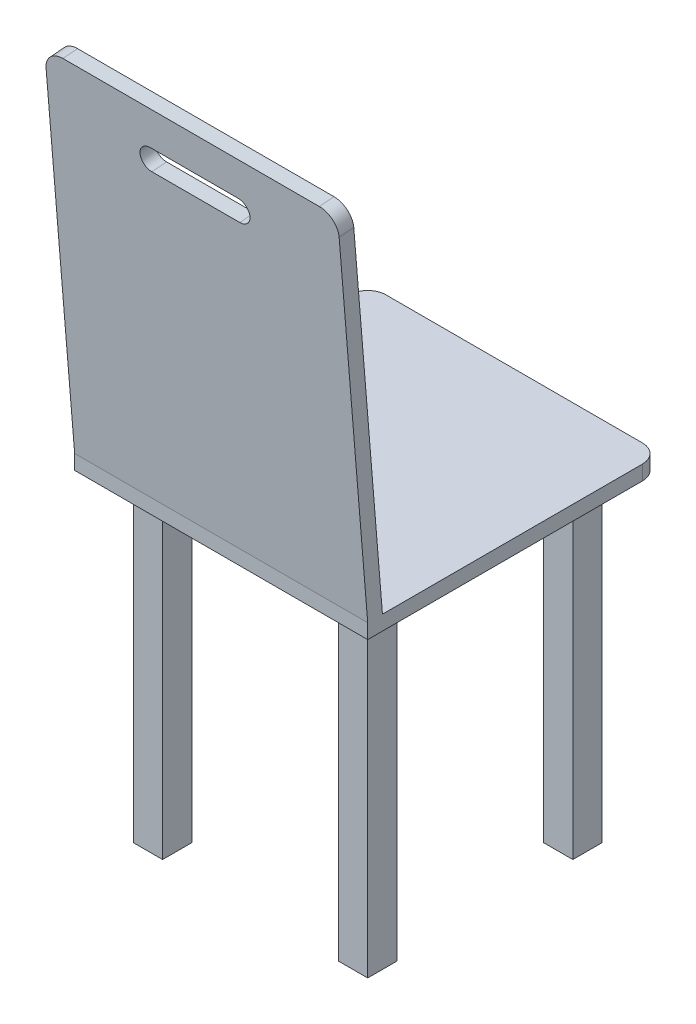
SolidWorks part; units mm, degrees
material "Beech"
ref_plane "Front Plane" through (0, 0, 0) normal (0, 0, 1) x (1, 0, 0)
ref_plane "Top Plane" through (0, 0, 0) normal (0, 1, 0) x (1, 0, 0)
ref_plane "Right Plane" through (0, 0, 0) normal (1, 0, 0) x (0, 0, -1)
sketch "Sketch3" plane through (0, 0, 0) normal (1, 0, 0) x (0, 0, -1)
  line L0 (0, 0) -> (40, 0)
  line L1 (40, 0) -> (40, 2)
  line L2 (40, 2) -> (2.0135, 2)
  line L3 (0, 2) -> (0, 0)
  line L4 (0, 2) -> (-4.1049, 52)
  line L5 (-4.1049, 52) -> (-2.1049, 52.1642)
  line L6 (-2.1049, 52.1642) -> (2.0135, 2)
  dimension "D1" = 40
  dimension "D2" = 50
  dimension "D3" = 2
  dimension "D4" = 2
extrude "Boss-Extrude2" add sketch "Sketch3" along normal blind 40
fillet "Fillet3" radius 2.5 4 edges at (40, 1, -40) (0, 1, -40) (0, 52.0821, 3.1049) (40, 52.0821, 3.1049)
sketch "Sketch5" plane through (0, 0.0134, -0.1631) normal (0, -0.0818, 0.9966) x (1, 0, 0)
  line L0 (14, 47.1615) -> (26, 47.1615)
  line L1 (26, 44.1615) -> (14, 44.1615)
  line L2 (0, 49.6615) -> (0, 1.9933) construction
  line L3 (40, 49.6615) -> (40, 1.9933) construction
  line L4 (37.5, 52.1615) -> (2.5, 52.1615) construction
  arc A0 (26, 47.1615) -> (26, 44.1615) centre (26, 45.6615) cw
  arc A1 (14, 44.1615) -> (14, 47.1615) centre (14, 45.6615) cw
  dimension "D1" = 12
  dimension "D2" = 14
  dimension "D3" = 14
  dimension "D4" = 5
  dimension "D5" = 3
extrude "Cut-Extrude2" cut sketch "Sketch5" against normal blind 3
sketch "Sketch6" plane through (0, 0, 0) normal (0, -1, 0) x (1, 0, 0)
  line L0 (40, 0) -> (40, -37.5) construction
  line L1 (36, -4) -> (32, -4)
  line L2 (36, -4) -> (36, -8)
  line L3 (36, -8) -> (32, -8)
  line L4 (32, -4) -> (32, -8)
  line L5 (40, 0) -> (0, 0) construction
  dimension "D1" = 4
  dimension "D2" = 4
  dimension "D3" = 4
  dimension "D4" = 4
extrude "Boss-Extrude3" add sketch "Sketch6" along normal blind 44
sketch "Sketch7" plane through (0, 0, 0) normal (0, -1, 0) x (1, 0, 0)
  line L0 (40, 0) -> (0, 0) construction
  line L1 (4, -4) -> (8, -4)
  line L2 (4, -4) -> (4, -8)
  line L3 (4, -8) -> (8, -8)
  line L4 (8, -4) -> (8, -8)
  line L5 (0, 0) -> (0, -37.5) construction
  point P4 (0, 0)
  dimension "D1" = 4
  dimension "D2" = 4
  dimension "D3" = 4
  dimension "D4" = 4
extrude "Boss-Extrude5" add sketch "Sketch7" along normal blind 44
sketch "Sketch8" plane through (0, 0, 0) normal (0, -1, 0) x (1, 0, 0)
  line L0 (37.5, -40) -> (2.5, -40) construction
  line L1 (4, -32) -> (8, -32)
  line L2 (4, -32) -> (4, -36)
  line L3 (4, -36) -> (8, -36)
  line L4 (8, -32) -> (8, -36)
  line L5 (0, 0) -> (0, -37.5) construction
  dimension "D1" = 4
  dimension "D2" = 4
  dimension "D3" = 4
  dimension "D4" = 4
extrude "Boss-Extrude6" add sketch "Sketch8" along normal blind 44
sketch "Sketch9" plane through (0, 0, 0) normal (0, -1, 0) x (1, 0, 0)
  line L0 (40, 0) -> (40, -37.5) construction
  line L1 (32, -32) -> (36, -32)
  line L2 (32, -32) -> (32, -36)
  line L3 (32, -36) -> (36, -36)
  line L4 (36, -32) -> (36, -36)
  line L5 (37.5, -40) -> (2.5, -40) construction
  dimension "D1" = 4
  dimension "D2" = 4
  dimension "D3" = 4
  dimension "D4" = 4
extrude "Boss-Extrude7" add sketch "Sketch9" along normal blind 44
